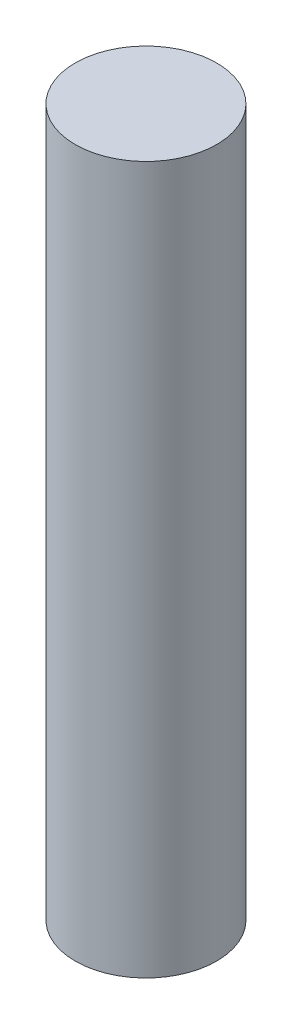
SolidWorks part; units mm, degrees
ref_plane "Front Plane" through (0, 0, 0) normal (0, 0, 1) x (1, 0, 0)
ref_plane "Top Plane" through (0, 0, 0) normal (0, 1, 0) x (1, 0, 0)
ref_plane "Right Plane" through (0, 0, 0) normal (1, 0, 0) x (0, 0, -1)
sketch "Sketch1" plane through (0, 0, 0) normal (0, 1, 0) x (1, 0, 0)
  circle A0 centre (0, 0) radius 5.08
  dimension "D1" = 10.16
extrude "Boss-Extrude1" add sketch "Sketch1" along normal blind 50.8
